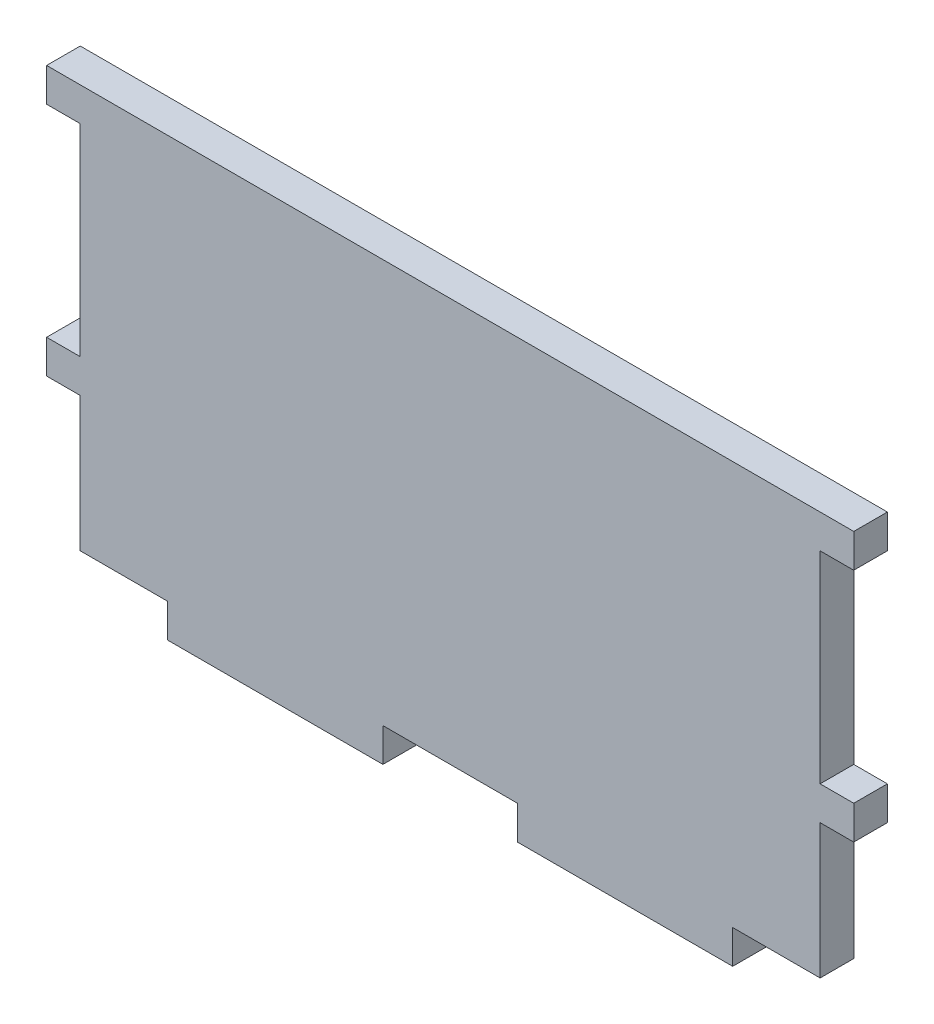
SolidWorks part; units mm, degrees
ref_plane "Front Plane" through (0, 0, 0) normal (0, 0, 1) x (1, 0, 0)
ref_plane "Top Plane" through (0, 0, 0) normal (0, 1, 0) x (1, 0, 0)
ref_plane "Right Plane" through (0, 0, 0) normal (1, 0, 0) x (0, 0, -1)
sketch "Sketch1" plane through (0, 0, 0) normal (0, 0, 1) x (1, 0, 0)
  line L1 (34.925, 19.05) -> (-34.925, 19.05)
  line L2 (34.925, 19.05) -> (34.925, -19.05)
  line L3 (34.925, -19.05) -> (-34.925, -19.05)
  line L4 (-34.925, 19.05) -> (-34.925, -19.05)
  line L5 (34.925, 19.05) -> (-34.925, -19.05) construction
  line L6 (34.925, -19.05) -> (-34.925, 19.05) construction
  point P0 (0, 0)
  point P5 (0, 0)
  dimension "D1" = 38.1
  dimension "D2" = 69.85
extrude "Boss-Extrude1" add sketch "Sketch1" along normal blind 3.175
sketch "Sketch2" plane through (0, 0, 0) normal (0, 0, -1) x (-1, 0, 0)
  line L0 (-34.925, -19.05) -> (-34.925, 19.05) construction
  line L1 (-38.1, 19.05) -> (-34.925, 19.05)
  line L2 (-38.1, 19.05) -> (-38.1, 15.875)
  line L3 (-38.1, 15.875) -> (-34.925, 15.875)
  line L4 (-34.925, 19.05) -> (-34.925, 15.875)
  line L5 (-38.1, 19.05) -> (-34.925, 15.875) construction
  line L6 (-38.1, 15.875) -> (-34.925, 19.05) construction
  line L7 (-38.1, -3.175) -> (-34.925, -3.175)
  line L8 (-38.1, -3.175) -> (-38.1, -6.35)
  line L9 (-38.1, -6.35) -> (-34.925, -6.35)
  line L10 (-34.925, -3.175) -> (-34.925, -6.35)
  line L11 (-38.1, -3.175) -> (-34.925, -6.35) construction
  line L12 (-38.1, -6.35) -> (-34.925, -3.175) construction
  line L13 (-34.925, 19.05) -> (34.925, 19.05) construction
  line L14 (34.925, -19.05) -> (-34.925, -19.05) construction
  line L15 (0.3737, 27.0265) -> (0.3737, 25.6393) construction
  line L16 (0, -24.5869) -> (0, 28.6528) construction
  line L17 (-34.925, -19.05) -> (-34.925, 19.05) construction
  line L19 (38.1, 15.875) -> (34.925, 19.05) construction
  line L20 (38.1, 19.05) -> (34.925, 15.875) construction
  line L21 (34.925, 19.05) -> (34.925, 15.875)
  line L22 (38.1, 15.875) -> (34.925, 15.875)
  line L23 (38.1, 19.05) -> (38.1, 15.875)
  line L24 (38.1, 19.05) -> (34.925, 19.05)
  line L25 (38.1, -6.35) -> (34.925, -3.175) construction
  line L26 (38.1, -3.175) -> (34.925, -6.35) construction
  line L27 (34.925, -3.175) -> (34.925, -6.35)
  line L28 (38.1, -6.35) -> (34.925, -6.35)
  line L29 (38.1, -3.175) -> (38.1, -6.35)
  line L30 (38.1, -3.175) -> (34.925, -3.175)
  point P0 (-36.5125, 17.4625)
  point P5 (-36.5125, -4.7625)
  point P26 (36.5125, 17.4625)
  point P31 (36.5125, -4.7625)
  dimension "D1" = 3.175
  dimension "D2" = 3.175
  dimension "D3" = 12.7
  dimension "D4" = 34.925
extrude "Boss-Extrude2" add sketch "Sketch2" against normal blind 3.175
sketch "Sketch3" plane through (0, -19.05, 0) normal (0, -1, 0) x (1, 0, 0)
  line L0 (0, 14.2531) -> (0, -11.7608) construction
  line L1 (-26.67, 3.175) -> (-6.35, 3.175)
  line L2 (-26.67, 3.175) -> (-26.67, 0)
  line L3 (-26.67, 0) -> (-6.35, 0)
  line L4 (-6.35, 3.175) -> (-6.35, 0)
  line L5 (-26.67, 3.175) -> (-6.35, 0) construction
  line L6 (-26.67, 0) -> (-6.35, 3.175) construction
  line L7 (-34.925, 0) -> (34.925, 0) construction
  line L8 (-34.925, 3.175) -> (34.925, 3.175) construction
  line L9 (26.67, 0) -> (6.35, 3.175) construction
  line L10 (26.67, 3.175) -> (6.35, 0) construction
  line L11 (6.35, 3.175) -> (6.35, 0)
  line L12 (26.67, 0) -> (6.35, 0)
  line L13 (26.67, 3.175) -> (26.67, 0)
  line L14 (26.67, 3.175) -> (6.35, 3.175)
  point P0 (-16.51, 1.5875)
  point P16 (16.51, 1.5875)
  dimension "D1" = 20.32
  dimension "D2" = 6.35
extrude "Boss-Extrude3" add sketch "Sketch3" along normal blind 3.175
